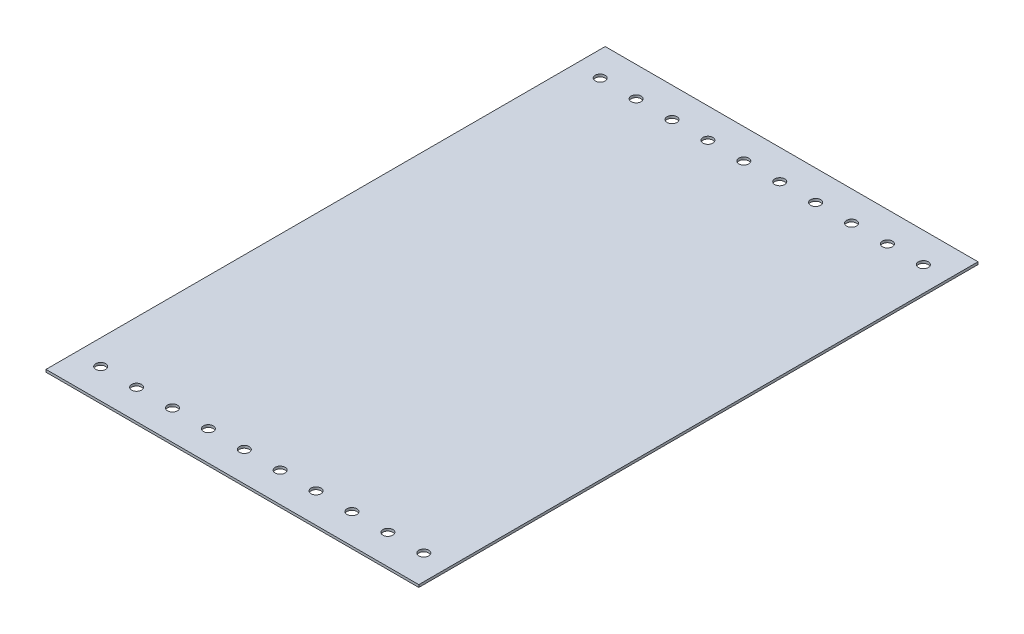
SolidWorks part; units mm, degrees
ref_plane "Front Plane" through (0, 0, 0) normal (0, 0, 1) x (1, 0, 0)
ref_plane "Top Plane" through (0, 0, 0) normal (0, 1, 0) x (1, 0, 0)
ref_plane "Right Plane" through (0, 0, 0) normal (1, 0, 0) x (0, 0, -1)
sketch "Sketch2" plane through (0, 0, 0) normal (0, 1, 0) x (1, 0, 0)
  line L1 (150, -225) -> (-150, -225)
  line L2 (150, -225) -> (150, 225)
  line L3 (150, 225) -> (-150, 225)
  line L4 (-150, -225) -> (-150, 225)
  line L5 (150, -225) -> (-150, 225) construction
  line L6 (150, 225) -> (-150, -225) construction
  point P0 (0, 0)
  dimension "D1" = 450
  dimension "D2" = 300
extrude "Boss-Extrude1" add sketch "Sketch2" along normal blind 2
sketch "Sketch3" plane through (0, 2, 0) normal (0, 1, 0) x (1, 0, 0)
  line L0 (-150, 0) -> (150, 0) construction
  line L1 (-150, 225) -> (-150, -225) construction
  line L2 (150, -225) -> (150, 225) construction
  line L3 (150, 225) -> (-150, 225) construction
  circle A0 centre (-130, 201) radius 4
  circle A1 centre (-101.1111, 201) radius 4
  circle A2 centre (-72.2222, 201) radius 4
  circle A3 centre (-43.3333, 201) radius 4
  circle A4 centre (-14.4444, 201) radius 4
  circle A5 centre (14.4444, 201) radius 4
  circle A6 centre (43.3333, 201) radius 4
  circle A7 centre (72.2222, 201) radius 4
  circle A8 centre (101.1111, 201) radius 4
  circle A9 centre (130, 201) radius 4
  circle A10 centre (130, -201) radius 4
  circle A11 centre (101.1111, -201) radius 4
  circle A12 centre (72.2222, -201) radius 4
  circle A13 centre (43.3333, -201) radius 4
  circle A14 centre (14.4444, -201) radius 4
  circle A15 centre (-14.4444, -201) radius 4
  circle A16 centre (-43.3333, -201) radius 4
  circle A17 centre (-72.2222, -201) radius 4
  circle A18 centre (-101.1111, -201) radius 4
  circle A19 centre (-130, -201) radius 4
  dimension "D1" = 8
  dimension "D2" = 20
  dimension "D3" = 24
  dimension "D5" = 20
  dimension "D4" = 10
extrude "Cut-Extrude1" cut sketch "Sketch3" against normal blind 2
